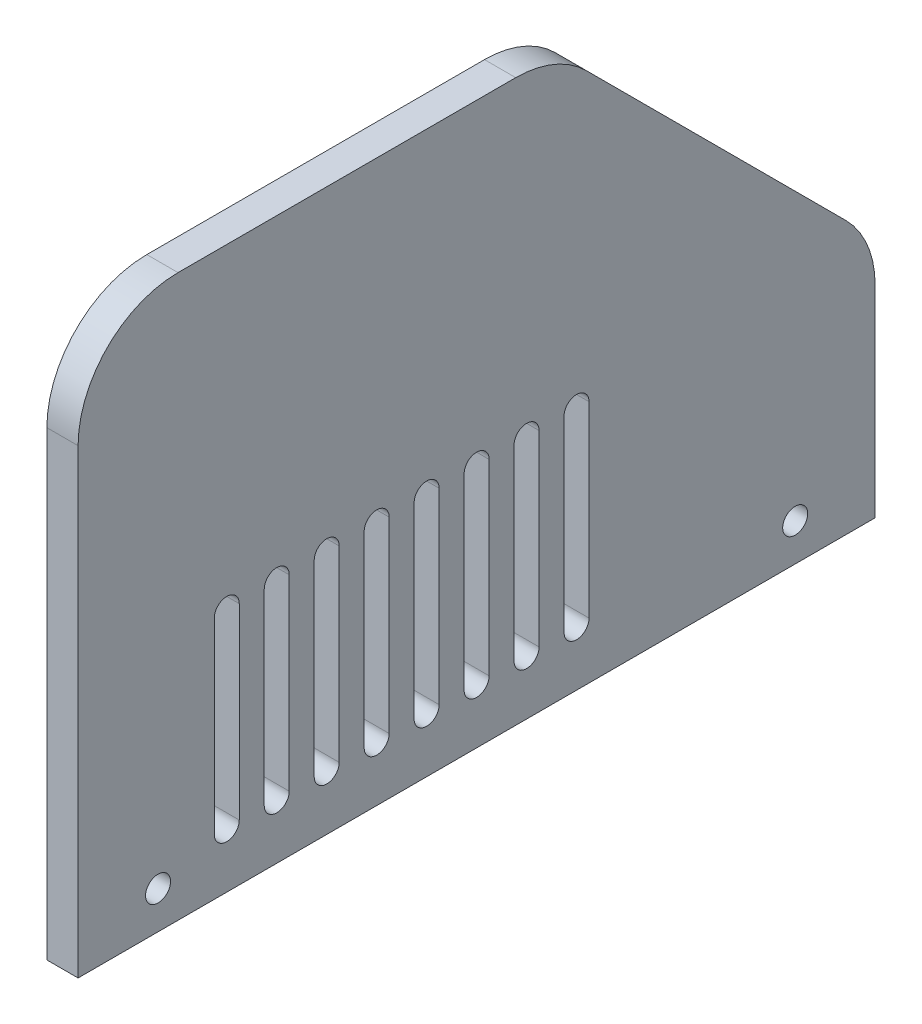
SolidWorks part; units mm, degrees
ref_plane "Front Plane" through (0, 0, 0) normal (0, 0, 1) x (1, 0, 0)
ref_plane "Top Plane" through (0, 0, 0) normal (0, 1, 0) x (1, 0, 0)
ref_plane "Right Plane" through (0, 0, 0) normal (1, 0, 0) x (0, 0, -1)
sketch "Sketch1" plane through (0, 0, 0) normal (1, 0, 0) x (0, 0, -1)
  line L0 (0, 0) -> (81.026, 0)
  line L1 (81.026, 0) -> (81.026, 24.6941)
  line L2 (81.026, 24.6941) -> (48.6971, 57.023)
  line L3 (48.6971, 57.023) -> (0, 57.023)
  line L4 (0, 57.023) -> (0, 0)
  line L5 (40.513, 24.765) -> (40.513, 5.715) construction
  line L6 (41.783, 24.765) -> (41.783, 5.715)
  line L7 (39.243, 24.765) -> (39.243, 5.715)
  line L8 (40.513, 0) -> (40.513, 57.023) construction
  line L9 (45.593, 24.765) -> (45.593, 5.715) construction
  line L10 (46.863, 24.765) -> (46.863, 5.715)
  line L11 (44.323, 24.765) -> (44.323, 5.715)
  line L12 (50.673, 24.765) -> (50.673, 5.715) construction
  line L13 (51.943, 24.765) -> (51.943, 5.715)
  line L14 (49.403, 24.765) -> (49.403, 5.715)
  line L18 (15.113, 24.765) -> (15.113, 5.715) construction
  line L21 (40.513, 24.765) -> (40.513, 5.715) construction
  line L22 (41.783, 24.765) -> (41.783, 5.715)
  line L23 (39.243, 24.765) -> (39.243, 5.715)
  line L24 (45.593, 24.765) -> (45.593, 5.715) construction
  line L25 (46.863, 24.765) -> (46.863, 5.715)
  line L26 (44.323, 24.765) -> (44.323, 5.715)
  line L30 (16.383, 24.765) -> (16.383, 5.715)
  line L33 (35.433, 24.765) -> (35.433, 5.715) construction
  line L34 (36.703, 24.765) -> (36.703, 5.715)
  line L35 (34.163, 24.765) -> (34.163, 5.715)
  line L36 (40.513, 24.765) -> (40.513, 5.715) construction
  line L37 (41.783, 24.765) -> (41.783, 5.715)
  line L38 (39.243, 24.765) -> (39.243, 5.715)
  line L42 (13.843, 24.765) -> (13.843, 5.715)
  line L45 (30.353, 24.765) -> (30.353, 5.715) construction
  line L46 (31.623, 24.765) -> (31.623, 5.715)
  line L47 (29.083, 24.765) -> (29.083, 5.715)
  line L48 (35.433, 24.765) -> (35.433, 5.715) construction
  line L49 (36.703, 24.765) -> (36.703, 5.715)
  line L50 (34.163, 24.765) -> (34.163, 5.715)
  line L54 (20.193, 24.765) -> (20.193, 5.715) construction
  line L57 (25.273, 24.765) -> (25.273, 5.715) construction
  line L58 (26.543, 24.765) -> (26.543, 5.715)
  line L59 (24.003, 24.765) -> (24.003, 5.715)
  line L60 (30.353, 24.765) -> (30.353, 5.715) construction
  line L61 (31.623, 24.765) -> (31.623, 5.715)
  line L62 (29.083, 24.765) -> (29.083, 5.715)
  line L66 (21.463, 24.765) -> (21.463, 5.715)
  line L69 (18.923, 24.765) -> (18.923, 5.715)
  line L72 (25.273, 24.765) -> (25.273, 5.715) construction
  line L75 (26.543, 24.765) -> (26.543, 5.715)
  line L78 (24.003, 24.765) -> (24.003, 5.715)
  line L93 (35.433, 24.765) -> (35.433, 5.715) construction
  line L94 (36.703, 24.765) -> (36.703, 5.715)
  line L95 (34.163, 24.765) -> (34.163, 5.715)
  line L96 (30.353, 24.765) -> (30.353, 5.715) construction
  line L97 (31.623, 24.765) -> (31.623, 5.715)
  line L98 (29.083, 24.765) -> (29.083, 5.715)
  line L99 (25.273, 24.765) -> (25.273, 5.715) construction
  line L100 (26.543, 24.765) -> (26.543, 5.715)
  line L101 (24.003, 24.765) -> (24.003, 5.715)
  line L102 (20.193, 24.765) -> (20.193, 5.715) construction
  line L103 (21.463, 24.765) -> (21.463, 5.715)
  line L104 (18.923, 24.765) -> (18.923, 5.715)
  arc A0 (41.783, 24.765) -> (39.243, 24.765) centre (40.513, 24.765) ccw
  arc A1 (39.243, 5.715) -> (41.783, 5.715) centre (40.513, 5.715) ccw
  arc A2 (46.863, 24.765) -> (44.323, 24.765) centre (45.593, 24.765) ccw
  arc A3 (44.323, 5.715) -> (46.863, 5.715) centre (45.593, 5.715) ccw
  arc A4 (51.943, 24.765) -> (49.403, 24.765) centre (50.673, 24.765) ccw
  arc A5 (49.403, 5.715) -> (51.943, 5.715) centre (50.673, 5.715) ccw
  arc A10 (41.783, 24.765) -> (39.243, 24.765) centre (40.513, 24.765) ccw
  arc A11 (39.243, 5.715) -> (41.783, 5.715) centre (40.513, 5.715) ccw
  arc A12 (46.863, 24.765) -> (44.323, 24.765) centre (45.593, 24.765) ccw
  arc A13 (44.323, 5.715) -> (46.863, 5.715) centre (45.593, 5.715) ccw
  arc A18 (36.703, 24.765) -> (34.163, 24.765) centre (35.433, 24.765) ccw
  arc A19 (34.163, 5.715) -> (36.703, 5.715) centre (35.433, 5.715) ccw
  arc A20 (41.783, 24.765) -> (39.243, 24.765) centre (40.513, 24.765) ccw
  arc A21 (39.243, 5.715) -> (41.783, 5.715) centre (40.513, 5.715) ccw
  arc A26 (31.623, 24.765) -> (29.083, 24.765) centre (30.353, 24.765) ccw
  arc A27 (29.083, 5.715) -> (31.623, 5.715) centre (30.353, 5.715) ccw
  arc A28 (36.703, 24.765) -> (34.163, 24.765) centre (35.433, 24.765) ccw
  arc A29 (34.163, 5.715) -> (36.703, 5.715) centre (35.433, 5.715) ccw
  arc A34 (26.543, 24.765) -> (24.003, 24.765) centre (25.273, 24.765) ccw
  arc A35 (24.003, 5.715) -> (26.543, 5.715) centre (25.273, 5.715) ccw
  arc A36 (31.623, 24.765) -> (29.083, 24.765) centre (30.353, 24.765) ccw
  arc A37 (29.083, 5.715) -> (31.623, 5.715) centre (30.353, 5.715) ccw
  arc A58 (36.703, 24.765) -> (34.163, 24.765) centre (35.433, 24.765) ccw
  arc A59 (34.163, 5.715) -> (36.703, 5.715) centre (35.433, 5.715) ccw
  arc A60 (31.623, 24.765) -> (29.083, 24.765) centre (30.353, 24.765) ccw
  arc A61 (29.083, 5.715) -> (31.623, 5.715) centre (30.353, 5.715) ccw
  arc A62 (26.543, 24.765) -> (24.003, 24.765) centre (25.273, 24.765) ccw
  arc A63 (24.003, 5.715) -> (26.543, 5.715) centre (25.273, 5.715) ccw
  arc A64 (21.463, 24.765) -> (18.923, 24.765) centre (20.193, 24.765) ccw
  arc A65 (18.923, 5.715) -> (21.463, 5.715) centre (20.193, 5.715) ccw
  arc A70 (16.383, 24.765) -> (13.843, 24.765) centre (15.113, 24.765) ccw
  arc A71 (13.843, 5.715) -> (16.383, 5.715) centre (15.113, 5.715) ccw
  arc A72 (21.463, 24.765) -> (18.923, 24.765) centre (20.193, 24.765) ccw
  arc A73 (18.923, 5.715) -> (21.463, 5.715) centre (20.193, 5.715) ccw
  arc A74 (26.543, 24.765) -> (24.003, 24.765) centre (25.273, 24.765) ccw
  arc A75 (24.003, 5.715) -> (26.543, 5.715) centre (25.273, 5.715) ccw
  circle A478 centre (8.128, 3.81) radius 1.27
  circle A479 centre (72.898, 3.81) radius 1.27
  point P8 (40.513, 15.24)
  point P17 (15.113, 15.24)
  point P20 (45.593, 15.24)
  point P27 (50.673, 15.24)
  point P45 (20.193, 15.24)
  point P48 (40.513, 15.24)
  point P55 (45.593, 15.24)
  point P73 (25.273, 15.24)
  point P76 (35.433, 15.24)
  point P83 (40.513, 15.24)
  point P104 (30.353, 15.24)
  point P111 (35.433, 15.24)
  point P132 (25.273, 15.24)
  point P139 (30.353, 15.24)
  point P216 (35.433, 15.24)
  point P223 (30.353, 15.24)
  point P230 (25.273, 15.24)
  point P237 (20.193, 15.24)
  dimension "D6" = 1.27
  dimension "D10" = 8.128
  dimension "D14" = 2.54
  dimension "D15" = 2.54
  dimension "D1" = 57.023
  dimension "D2" = 81.026
  dimension "D3" = 135
  dimension "D4" = 45.72
  dimension "D5" = 19.05
  dimension "D7" = 15.24
  dimension "D8" = 3
  dimension "D11" = 8.128
  dimension "D12" = 3.81
  dimension "D13" = 3.81
  dimension "D9" = 6
extrude "Boss-Extrude1" add sketch "Sketch1" along normal blind 3.175
fillet "Fillet1" radius 10.16 3 edges at (1.5875, 24.6941, -81.026) (1.5875, 57.023, -48.6971) (1.5875, 57.023, 0)
